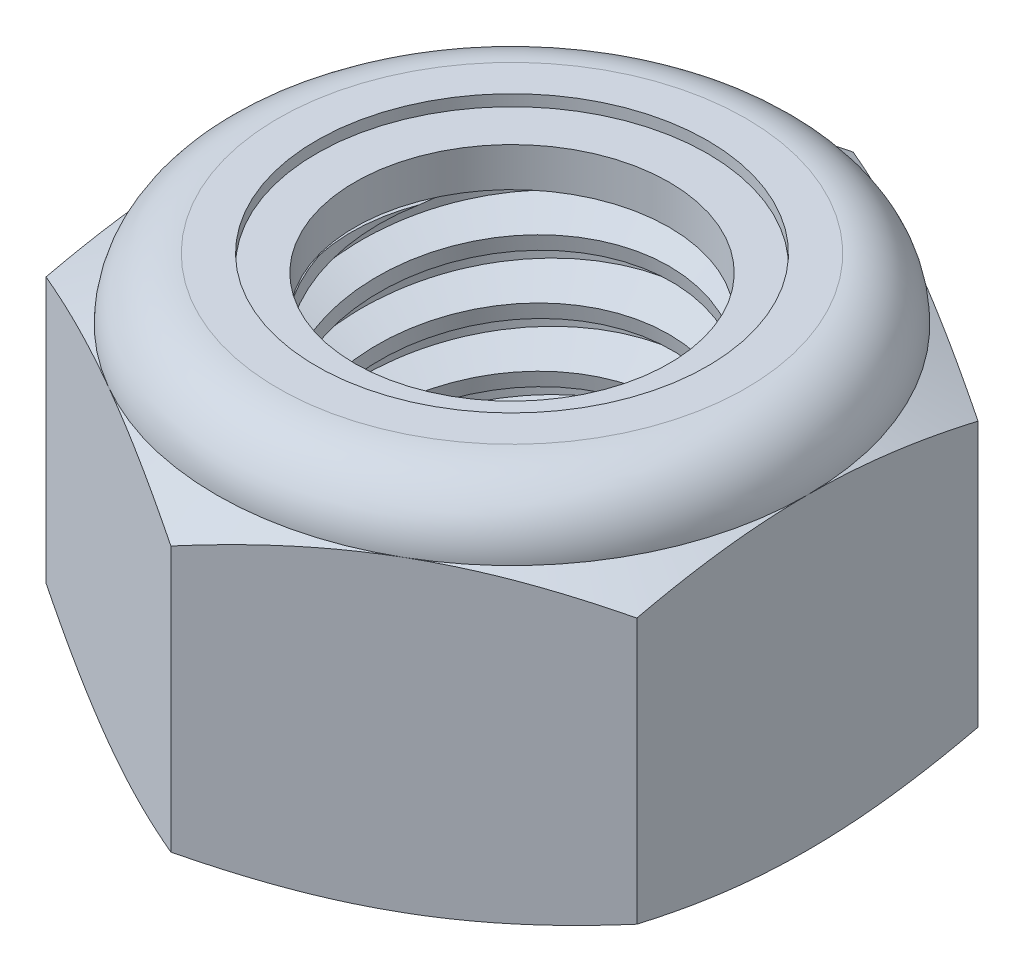
SolidWorks part; units mm, degrees
ref_plane "Front" through (0, 0, 0) normal (0, 0, 1) x (1, 0, 0)
ref_plane "Top" through (0, 0, 0) normal (0, 1, 0) x (1, 0, 0)
ref_plane "Right" through (0, 0, 0) normal (1, 0, 0) x (0, 0, -1)
sketch "Sketch1" plane through (0, 0, 0) normal (0, 1, 0) x (1, 0, 0)
  line L1 (0, 4.6188) -> (-4, 2.3094)
  line L2 (-4, 2.3094) -> (-4, -2.3094)
  line L3 (-4, -2.3094) -> (0, -4.6188)
  line L4 (0, -4.6188) -> (4, -2.3094)
  line L5 (4, -2.3094) -> (4, 2.3094)
  line L6 (4, 2.3094) -> (0, 4.6188)
  circle A0 centre (0, 0) radius 4 construction
  dimension "Hex Flats" = 8
extrude "Extrude1" add sketch "Sketch1" along normal blind 5
sketch "Sketch2" plane through (0, 0, 0) normal (1, 0, 0) x (0, 0, -1)
  line L0 (-2.5, 0) -> (-2.5, 5) construction
  line L1 (0, 0) -> (2.5, 0)
  line L2 (0, 0) -> (0, 5)
  line L3 (0, 5) -> (2.5, 5)
  line L4 (2.5, 0) -> (2.5, 5)
  line L5 (-2.3094, 5) -> (2.3094, 5) construction
  line L7 (0, -2.5) -> (0, 0) construction
  dimension "Thread Dia" = 5
revolve "Revolve1" add sketch "Sketch2" angle 360 about L7
sketch "Sketch3" plane through (0, 0, 0) normal (1, 0, 0) x (0, 0, -1)
  line L0 (2.5, 5) -> (-2.5, 5) construction
  line L1 (-2.5, 5) -> (-2.5, 4.2) construction
  line L2 (-2.5, 4.2) -> (2.5, 5) construction
  line L3 (2.5, 5) -> (2.5158, 4.9013) construction
  line L4 (2.5158, 4.9013) -> (2.6264, 4.21)
  line L5 (2.6264, 4.21) -> (2.1593, 4.3885)
  line L6 (2.1593, 4.3885) -> (2.1277, 4.586)
  line L7 (2.1277, 4.586) -> (2.5158, 4.9013)
  line L8 (2.1435, 4.4872) -> (2.5711, 4.5557) construction
  line L9 (2.5, 5) -> (2.5, 4.5443) construction
  line L10 (2.5, 4.5443) -> (-2.5, 3.7443) construction
  line L11 (-2.5, 3.7443) -> (-2.5, 4.2) construction
  line L12 (-0.1369, 5) -> (0.1369, 3.2886) construction
  line L13 (-2.5, 0) -> (-2.5, 5) construction
  line L14 (0, 5) -> (2.5, 5) construction
  line L15 (2.5, 0) -> (2.5, 5) construction
  point P13 (0, 4.1443)
  dimension "D1" = 0.1
  dimension "D2" = 0.2
  dimension "Thread Pitch" = 0.8
  dimension "D4" = 60
  dimension "D5" = 0.8
revolve "Cut-Revolve1" cut sketch "Sketch3" angle 360 about L12
pattern_linear "LPattern1" count 6 spacing 0.8 along (0, -1, 0) count 2 spacing 0.8 along (0, 1, 0) of "Cut-Revolve1"
sketch "Sketch4" plane through (0, 0, 0) normal (1, 0, 0) x (0, 0, -1)
  line L0 (0, 5) -> (2.5, 5)
  line L1 (2.5, 5) -> (2.1277, 4.8264)
  line L2 (2.1277, 4.8264) -> (2.1277, 0.1736)
  line L3 (2.1277, 0.1736) -> (2.5, 0)
  line L4 (2.5, 0) -> (0, 0)
  line L5 (0, 0) -> (0, 5)
  line L6 (2.5, 0) -> (2.5, 5) construction
  line L7 (0, 5) -> (2.5, 5) construction
  line L8 (0, 0) -> (2.5, 0) construction
  line L9 (0, 0) -> (0, 5) construction
  line L10 (0, 5) -> (0, 5.4108) construction
  dimension "D1" = 25
revolve "Cut-Revolve2" cut sketch "Sketch4" angle 360 about L10
combine bodies "Combine1" operation type subtract main body 112 bodies to subtract 111
sketch "Sketch5" plane through (0, 0, 0) normal (1, 0, 0) x (0, 0, -1)
  line L0 (0, 0) -> (4, 0)
  line L1 (4, 0) -> (4.6188, 0.2886)
  line L2 (4.6188, 0.2886) -> (4.6188, 3.8781)
  line L3 (4.6188, 3.8781) -> (4, 4.1667)
  line L4 (3.1667, 5) -> (3.1667, 6.27)
  line L5 (3.1667, 6.27) -> (5.8888, 6.27)
  line L6 (5.8888, 6.27) -> (5.8888, -1.27)
  line L7 (5.8888, -1.27) -> (0, -1.27)
  line L8 (0, -1.27) -> (0, 0)
  line L9 (4, 4.1667) -> (4, 0) construction
  line L10 (0, 0) -> (2.5, 0) construction
  line L13 (4.6188, 2.0833) -> (5.8888, 2.0833) construction
  line L14 (4.6188, 5) -> (4.6188, 0) construction
  line L15 (0, 0) -> (0, 6.27) construction
  line L20 (0, 6.27) -> (3.1667, 6.27) construction
  line L22 (0, 5) -> (2.5, 5) construction
  arc A0 (4, 4.1667) -> (3.1667, 5) centre (3.1667, 4.1667) ccw
  dimension "D1" = 25
  dimension "D2" = 1.27
  dimension "D3" = 5
  dimension "D4" = 0.8333
revolve "Cut-Revolve3" cut sketch "Sketch5" angle 360 about L15
sketch "Sketch6" plane through (0, 0, 0) normal (1, 0, 0) x (0, 0, -1)
  line L0 (0, 4.1667) -> (3.8476, 4.1667)
  line L1 (3.1667, 4.8476) -> (2.6472, 4.8476)
  line L2 (0, 6.27) -> (0, 4.1667)
  line L3 (2.6472, 6.27) -> (0, 6.27)
  line L4 (0, 6.27) -> (3.1667, 6.27) construction
  line L5 (0, 0) -> (0, 6.27) construction
  line L6 (0, 6.27) -> (0, 44.323) construction
  line L7 (2.6472, 4.8476) -> (2.6472, 6.27)
  line L8 (3.1667, 5) -> (3.1667, 4.8476) construction
  line L9 (2.6472, 4.8476) -> (2.1277, 4.8476) construction
  line L10 (2.1277, 4.8476) -> (2.1277, 4.8264) construction
  arc A0 (3.8476, 4.1667) -> (3.1667, 4.8476) centre (3.1667, 4.1667) ccw
  arc A1 (4, 4.1667) -> (3.1667, 5) centre (3.1667, 4.1667) ccw construction
  dimension "D1" = 0.1524
revolve "Cut-Revolve4" cut sketch "Sketch6" angle 360 about L6
sketch "Sketch7" plane through (0, 0, 0) normal (1, 0, 0) x (0, 0, -1)
  line L0 (2.1277, 4.2429) -> (3.7666, 4.2429)
  line L1 (3.1667, 4.7714) -> (2.1277, 4.7714)
  line L2 (2.1277, 4.7714) -> (2.1277, 4.2429)
  line L3 (2.1277, 4.2429) -> (0, 4.2429) construction
  line L4 (0, 4.2429) -> (0, 4.7714) construction
  line L5 (0, 4.7714) -> (2.1277, 4.7714) construction
  line L6 (2.1277, 4.2429) -> (2.1277, 4.1667) construction
  line L7 (0, 4.1667) -> (3.8476, 4.1667) construction
  line L8 (3.1667, 4.7714) -> (3.1667, 4.8476) construction
  arc A0 (3.7666, 4.2429) -> (3.1667, 4.7714) centre (3.1667, 4.1667) ccw
  arc A2 (3.8476, 4.1667) -> (3.1667, 4.8476) centre (3.1667, 4.1667) ccw construction
  dimension "D1" = 0.0762
revolve "Revolve2" add sketch "Sketch7" angle 360 about L4
equation "\"D1@Sketch3\"=\"Thread Pitch@Sketch3\"/8"
equation "\"D2@Sketch3\"=\"Thread Pitch@Sketch3\"/4"
equation "\"D5@Sketch3\"=\"Thread Pitch@Sketch3\""
equation "\"D4@LPattern1\"=\"Thread Pitch@Sketch3\""
equation "\"D3@LPattern1\"=\"Thread Pitch@Sketch3\""
equation "\"D1@LPattern1\"=\"Height@Extrude1\"/\"Thread Pitch@Sketch3\""
equation "\"D4@Sketch5\"=\"Height@Extrude1\"/6"
